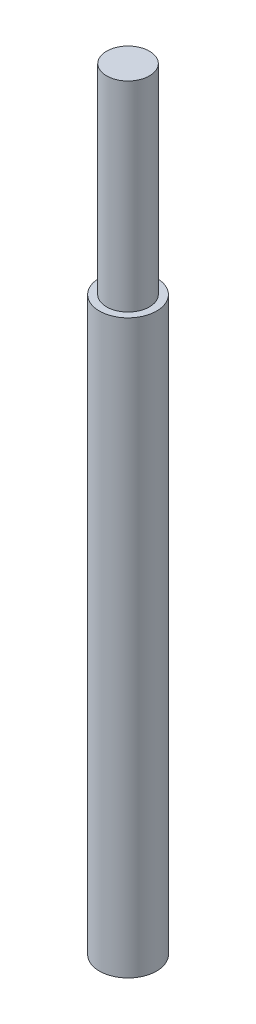
SolidWorks part; units mm, degrees
material "ASTM A36 Acero"
ref_plane "Alzado" through (0, 0, 0) normal (0, 0, 1) x (1, 0, 0)
ref_plane "Planta" through (0, 0, 0) normal (0, 1, 0) x (1, 0, 0)
ref_plane "Vista lateral" through (0, 0, 0) normal (1, 0, 0) x (0, 0, -1)
sketch "Croquis1" plane through (0, 0, 0) normal (0, 1, 0) x (1, 0, 0)
  circle A0 centre (0, 0) radius 7.5
  dimension "D1" = 15
extrude "Saliente-Extruir1" add sketch "Croquis1" along normal blind 70
sketch "Croquis2" plane through (0, 0, 0) normal (0, -1, 0) x (1, 0, 0)
  circle A0 centre (0, 0) radius 10
  dimension "D1" = 20
extrude "Saliente-Extruir2" add sketch "Croquis2" along normal blind 200
